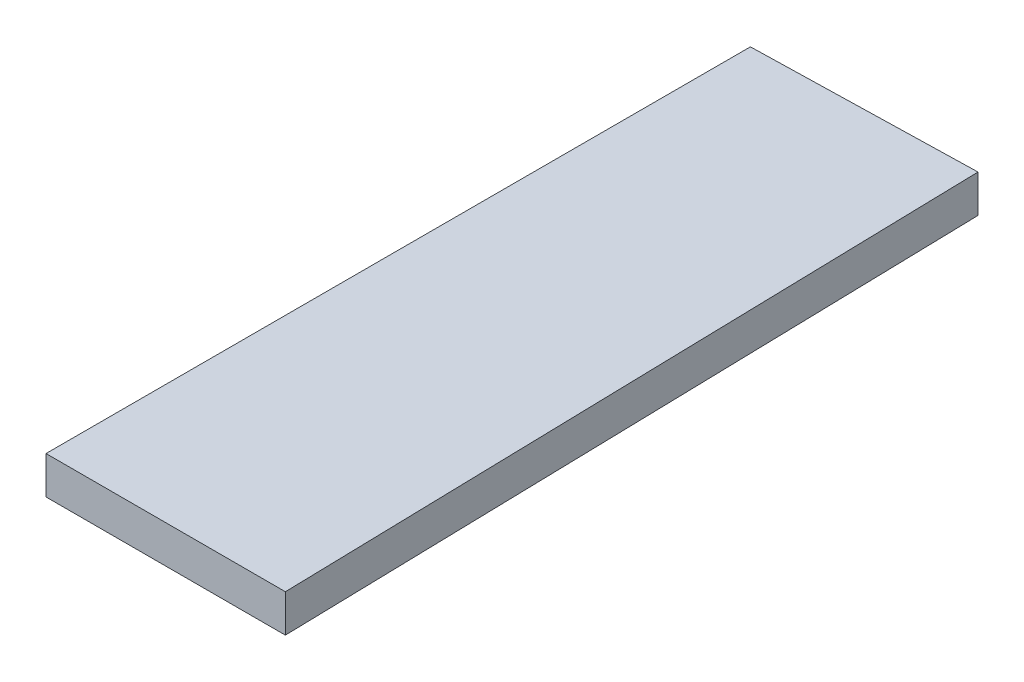
SolidWorks part; units mm, degrees
ref_plane "Plan de face" through (0, 0, 0) normal (0, 0, 1) x (1, 0, 0)
ref_plane "Plan de dessus" through (0, 0, 0) normal (0, 1, 0) x (1, 0, 0)
ref_plane "Plan de droite" through (0, 0, 0) normal (1, 0, 0) x (0, 0, -1)
sketch "Esquisse1" plane through (0, 0, 0) normal (0, 1, 0) x (1, 0, 0)
  line L0 (0, 0) -> (12.7235, 0)
  line L1 (12.7235, 0) -> (11.8105, 37.7257)
  line L2 (11.8105, 37.7257) -> (0, 37.4399)
  line L3 (0, 37.4399) -> (0, 0)
  point P4 (0, 0)
extrude "Boss.-Extru.1" add sketch "Esquisse1" along normal blind 2
